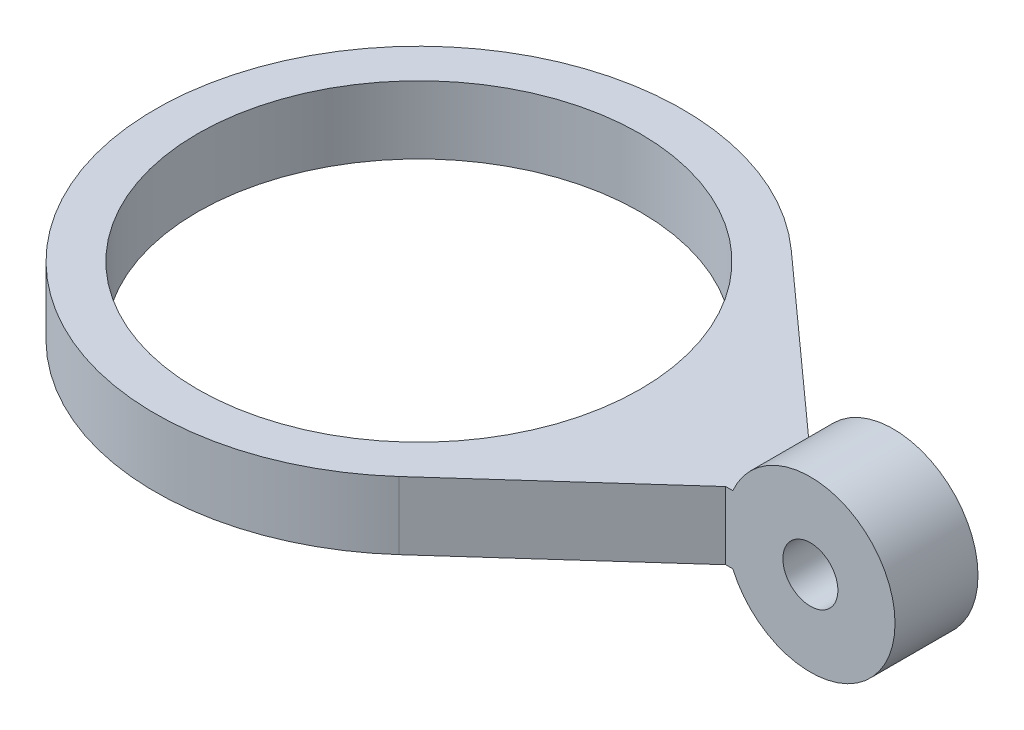
SolidWorks part; units mm, degrees
ref_plane "Alzado" through (0, 0, 0) normal (0, 0, 1) x (1, 0, 0)
ref_plane "Planta" through (0, 0, 0) normal (0, 1, 0) x (1, 0, 0)
ref_plane "Vista lateral" through (0, 0, 0) normal (1, 0, 0) x (0, 0, -1)
sketch "Croquis1" plane through (0, 0, 0) normal (0, 1, 0) x (1, 0, 0)
  circle A0 centre (0, 0) radius 13.075
  circle A1 centre (0, 0) radius 15.575
  dimension "D1" = 26.15
  dimension "D2" = 2.5
extrude "Saliente-Extruir1" add sketch "Croquis1" along normal blind 4
sketch "Croquis2" plane through (0, 0, 0) normal (0, 1, 0) x (1, 0, 0)
  line L0 (15.575, 19.4517) -> (15.575, -24.1563) construction
  line L1 (20.575, 0) -> (0, 0) construction
  line L2 (20.575, 2.45) -> (10.4106, 11.5844)
  line L4 (20.575, 2.45) -> (20.575, -2.45)
  line L6 (10.4106, -11.5844) -> (20.575, -2.45)
  circle A0 centre (0, 0) radius 15.575 construction
  arc A1 (10.4106, -11.5844) -> (10.4106, 11.5844) centre (0, 0) ccw
  dimension "D1" = 5
  dimension "D2" = 4.9
extrude "Saliente-Extruir2" add sketch "Croquis2" along normal up to surface (4 mm away) up to face at (0, 4, 15.575)
sketch "Croquis3" plane through (0, 0, 0) normal (0, 0, 1) x (1, 0, 0)
  line L0 (20.575, 2) -> (25.575, 2) construction
  line L3 (20.575, 4) -> (20.575, 0) construction
  line L4 (20.575, 4) -> (20.575, 0)
  line L5 (20.575, 0) -> (20.9924, 0)
  line L7 (20.9924, 4) -> (20.575, 4)
  arc A0 (20.9924, 0) -> (20.9924, 4) centre (25.575, 2) ccw
  dimension "D1" = 10
extrude "Saliente-Extruir3" add sketch "Croquis3" along normal mid plane 4.9
sketch "Croquis4" plane through (0, 0, 2.45) normal (0, 0, 1) x (1, 0, 0)
  circle A0 centre (25.575, 2) radius 1.625
  circle A1 centre (25.575, 2) radius 5 construction
  dimension "D1" = 3.25
extrude "Cortar-Extruir1" cut sketch "Croquis4" against normal through all
sketch "Croquis5" plane through (0, 4, 0) normal (0, 1, 0) x (1, 0, 0)
  line L0 (0, 0) -> (-14.6357, 5.327)
  line L1 (0, 0) -> (-15.575, 0) construction
  line L2 (-14.6357, -5.327) -> (0, 0)
  circle A0 centre (0, 0) radius 15.575 construction
  arc A1 (-14.6357, 5.327) -> (-14.6357, -5.327) centre (0, 0) ccw
  dimension "D1" = 20
  dimension "D2" = 20
extrude "Cortar-Extruir2" [suppressed] cut sketch "Croquis5" against normal through all
